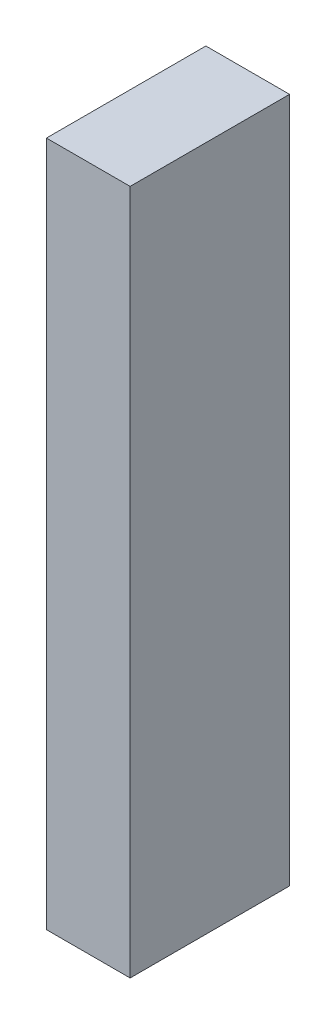
SolidWorks part; units mm, degrees
material "Polyester Resin"
ref_plane "Front Plane" through (0, 0, 0) normal (0, 0, 1) x (1, 0, 0)
ref_plane "Top Plane" through (0, 0, 0) normal (0, 1, 0) x (1, 0, 0)
ref_plane "Right Plane" through (0, 0, 0) normal (1, 0, 0) x (0, 0, -1)
sketch "Sketch1" plane through (0, 0, 0) normal (1, 0, 0) x (0, 0, -1)
  line L1 (-20, 86) -> (20, 86)
  line L2 (-20, 86) -> (-20, -86)
  line L3 (-20, -86) -> (20, -86)
  line L4 (20, 86) -> (20, -86)
  line L5 (0, -86) -> (0, 86) construction
  line L6 (-20, 0) -> (20, 0) construction
  point P0 (0, 0)
  dimension "D1" = 40
  dimension "D2" = 172
extrude "Boss-Extrude1" add sketch "Sketch1" along normal blind 21 contours L1 L4 L3 L2
